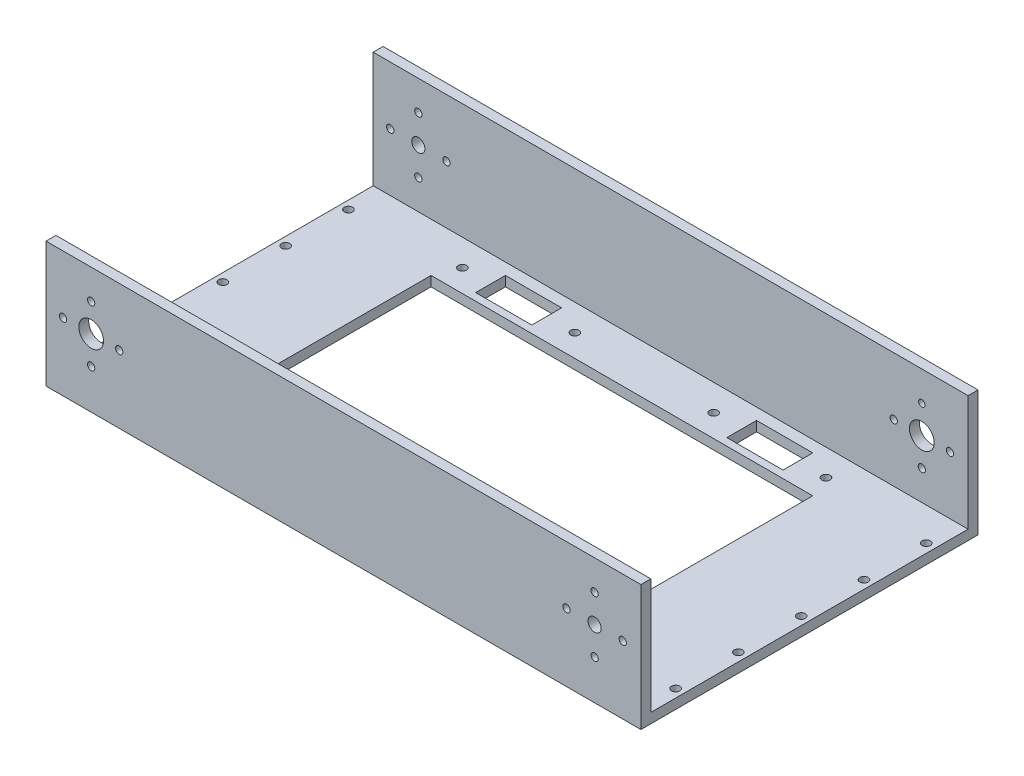
SolidWorks part; units mm, degrees
ref_plane "Front Plane" through (0, 0, 0) normal (0, 0, 1) x (1, 0, 0)
ref_plane "Top Plane" through (0, 0, 0) normal (0, 1, 0) x (1, 0, 0)
ref_plane "Right Plane" through (0, 0, 0) normal (1, 0, 0) x (0, 0, -1)
sketch "스케치1" plane through (0, 0, 0) normal (0, 0, 1) x (1, 0, 0)
  line L1 (-90, 17.5) -> (90, 17.5)
  line L2 (-90, 17.5) -> (-90, -17.5)
  line L3 (-90, -17.5) -> (90, -17.5)
  line L4 (90, 17.5) -> (90, -17.5)
  dimension "D1" = 17.5
  dimension "D2" = 35
  dimension "D3" = 90
  dimension "D4" = 180
extrude "보스-돌출1" add sketch "스케치1" along normal blind 3
sketch "스케치2" plane through (0, 0, 3) normal (0, 0, 1) x (1, 0, 0)
  line L0 (0, 0) -> (50000, 0) construction
  line L1 (0, 0) -> (0, -50000) construction
  line L2 (-76, 0) -> (-76, -50000) construction
  line L3 (76, 0) -> (76, -50000) construction
  circle A0 centre (-76.34, 0) radius 3.75
  circle A1 centre (76, 0) radius 2
  dimension "D3" = 7.5
  dimension "D4" = 4
  dimension "D1" = 76
  dimension "D2" = 76
extrude "컷-돌출1" cut sketch "스케치2" against normal blind 3
sketch "스케치3" plane through (0, 0, 3) normal (0, 0, 1) x (1, 0, 0)
  line L0 (-76.34, 0) -> (-76.34, 50000) construction
  line L1 (76, 0) -> (76, 50000) construction
  line L2 (-76.34, 0) -> (49923.66, 0) construction
  circle A0 centre (-76.34, 0) radius 8.5 construction
  circle A1 centre (76, 0) radius 8.5 construction
  circle A2 centre (-76.34, 8.5) radius 1.1
  circle A3 centre (-76.34, -8.5) radius 1.1
  circle A4 centre (-84.84, 0) radius 1.1
  circle A5 centre (-67.84, 0) radius 1.1
  circle A6 centre (76, 8.5) radius 1.1
  circle A7 centre (76, -8.5) radius 1.1
  circle A8 centre (67.5, 0) radius 1.1
  circle A9 centre (84.5, 0) radius 1.1
extrude "컷-돌출2" cut sketch "스케치3" against normal blind 3
sketch "스케치4" plane through (0, -17.5, 0) normal (0, -1, 0) x (1, 0, 0)
  line L0 (-90, 0) -> (-90, 50000) construction
  line L1 (90, 0) -> (90, 50000) construction
  line L2 (-100, 3) -> (49900, 3) construction
  line L6 (-100, -96) -> (49900, -96) construction
  line L7 (-100, -99) -> (49900, -99) construction
  line L8 (-100, 0) -> (49900, 0) construction
  line L11 (90, 3) -> (-90, 3)
  line L12 (90, 3) -> (90, -99)
  line L13 (90, -99) -> (-90, -99)
  line L14 (-90, 3) -> (-90, -99)
  dimension "D1" = 3
  dimension "D2" = 96
extrude "보스-돌출2" add sketch "스케치4" along normal blind 3
sketch "스케치5" plane through (0, -17.5, 0) normal (0, 1, 0) x (1, 0, 0)
  line L0 (-100, 99) -> (49900, 99) construction
  line L1 (86.532, 96) -> (50086.532, 96) construction
  line L2 (-90, 0) -> (-90, 50000) construction
  line L3 (-90, 0) -> (-90, 99) construction
  line L4 (90, 0) -> (90, 50000) construction
  line L7 (-90, 99) -> (90, 99)
  line L8 (-90, 99) -> (-90, 96)
  line L9 (-90, 96) -> (90, 96)
  line L10 (90, 99) -> (90, 96)
  dimension "D1" = 3
extrude "보스-돌출3" add sketch "스케치5" along normal blind 35
sketch "스케치6" plane through (0, 0, -99) normal (0, 0, -1) x (-1, 0, 0)
  circle A0 centre (-76, 0) radius 3.75
  circle A1 centre (76.34, 0) radius 2
  circle A2 centre (-76, -8.5) radius 1.1
  circle A3 centre (-67.5, 0) radius 1.1
  circle A4 centre (-76, 8.5) radius 0.9817
  circle A5 centre (-84.5, 0) radius 1.1
  circle A6 centre (84.84, 0) radius 1.1
  circle A7 centre (76.34, 8.5) radius 1.1
  circle A8 centre (67.84, 0) radius 1.1
  circle A9 centre (76.34, -8.5) radius 1.1
  dimension "D1" = 4
extrude "컷-돌출3" cut sketch "스케치6" against normal blind 35
sketch "스케치9" plane through (0, -17.5, 0) normal (0, 1, 0) x (1, 0, 0)
  line L0 (-0.8224, 48) -> (49999.1776, 48) construction
  line L1 (0, 0) -> (0, 50000) construction
  line L2 (90, 0) -> (-90, 0) construction
  line L4 (-57.75, 81.25) -> (57.75, 81.25)
  line L5 (-57.75, 81.25) -> (-57.75, 14.75)
  line L6 (-57.75, 14.75) -> (57.75, 14.75)
  line L7 (57.75, 81.25) -> (57.75, 14.75)
  dimension "D1" = 48
  dimension "D2" = 66.5
  dimension "D3" = 115.5
  dimension "D4" = 57.75
  dimension "D5" = 33.25
extrude "컷-돌출4" cut sketch "스케치9" against normal blind 10
sketch "스케치10" plane through (0, -20.5, 0) normal (0, -1, 0) x (1, 0, 0)
  line L0 (-10.9491, -48) -> (49989.0509, -48) construction
  line L1 (0, -34.9167) -> (0, -50034.9167) construction
  line L2 (-55, -10.9771) -> (-55, -50010.9771) construction
  line L3 (55, 8.1375) -> (55, -49991.8625) construction
  line L4 (-54.3745, -8) -> (49945.6255, -8) construction
  line L5 (75.9016, -88) -> (50075.9016, -88) construction
  line L6 (-90, 3) -> (-90, -99) construction
  line L7 (-90, -96) -> (90, -96) construction
  circle A0 centre (-55, -8) radius 1.25
  circle A1 centre (55, -8) radius 1.25
  circle A2 centre (55, -88) radius 1.25
  circle A3 centre (-55, -88) radius 1.25
  dimension "D1" = 90
  dimension "D2" = 48
  dimension "D3" = 55
  dimension "D4" = 55
  dimension "D5" = 40
  dimension "D6" = 40
extrude "컷-돌출5" cut sketch "스케치10" against normal blind 10
sketch "스케치11" plane through (0, -20.5, 0) normal (0, -1, 0) x (1, 0, 0)
  line L0 (55, -8) -> (-49945, -8) construction
  line L1 (55, -8) -> (55, -50008) construction
  line L2 (-55, -88) -> (-55, 49912) construction
  line L3 (-55, -88) -> (49945, -88) construction
  line L4 (38, -39.7065) -> (38, -50039.7065) construction
  line L5 (-38, -46.9547) -> (-38, -50046.9547) construction
  line L6 (21, -25.4517) -> (21, -50025.4517) construction
  line L7 (-21, -44.297) -> (-21, -50044.297) construction
  line L9 (46.5, -83.5) -> (29.5, -83.5)
  line L10 (46.5, -83.5) -> (46.5, -92.5)
  line L11 (46.5, -92.5) -> (29.5, -92.5)
  line L12 (29.5, -83.5) -> (29.5, -92.5)
  line L13 (-29.5, -83.5) -> (-46.5, -83.5)
  line L14 (-29.5, -83.5) -> (-29.5, -92.5)
  line L15 (-29.5, -92.5) -> (-46.5, -92.5)
  line L16 (-46.5, -83.5) -> (-46.5, -92.5)
  line L17 (46.5, -3.5) -> (29.5, -3.5)
  line L18 (46.5, -3.5) -> (46.5, -12.5)
  line L19 (46.5, -12.5) -> (29.5, -12.5)
  line L20 (29.5, -3.5) -> (29.5, -12.5)
  line L21 (-29.5, -3.5) -> (-46.5, -3.5)
  line L22 (-29.5, -3.5) -> (-29.5, -12.5)
  line L23 (-29.5, -12.5) -> (-46.5, -12.5)
  line L24 (-46.5, -3.5) -> (-46.5, -12.5)
  circle A0 centre (21, -8) radius 1.25
  circle A1 centre (-21, -8) radius 1.25
  circle A2 centre (21, -88) radius 1.25
  circle A3 centre (-21, -88) radius 1.25
  dimension "D5" = 17
  dimension "D1" = 17
  dimension "D2" = 17
  dimension "D3" = 17
  dimension "D4" = 17
  dimension "D6" = 9
  dimension "D7" = 9
  dimension "D8" = 17
  dimension "D9" = 17
  dimension "D10" = 9
  dimension "D11" = 17
  dimension "D12" = 9
  dimension "D13" = 8.5
  dimension "D14" = 4.5
  dimension "D15" = 4.5
  dimension "D16" = 8.5
  dimension "D17" = 4.5
  dimension "D18" = 8.5
  dimension "D19" = 8.5
  dimension "D20" = 4.5
extrude "컷-돌출6" cut sketch "스케치11" against normal blind 10
sketch "스케치12" plane through (0, -17.5, 0) normal (0, 1, 0) x (1, 0, 0)
  line L0 (-109.1605, 48) -> (49890.8395, 48) construction
  line L1 (-127.9882, 67) -> (49872.0118, 67) construction
  line L2 (-128.3888, 10) -> (49871.6112, 10) construction
  line L3 (-116.1709, 29) -> (49883.8291, 29) construction
  line L4 (-111.9647, 86) -> (49888.0353, 86) construction
  line L5 (-87.5, 63.4227) -> (-87.5, -49936.5773) construction
  line L6 (87.5, 65.6259) -> (87.5, -49934.3741) construction
  line L7 (90, 0) -> (-90, 0) construction
  line L9 (-90, 0) -> (-90, 96) construction
  line L10 (90, 96) -> (90, 0) construction
  circle A0 centre (-87.5, 86) radius 1.25
  circle A1 centre (-87.5, 67) radius 1.25
  circle A2 centre (-87.5, 48) radius 1.25
  circle A3 centre (-87.5, 29) radius 1.25
  circle A4 centre (-87.5, 10) radius 1.25
  circle A5 centre (87.3284, 86) radius 1.25
  circle A6 centre (87.5, 67) radius 1.25
  circle A7 centre (87.5, 48) radius 1.25
  circle A8 centre (87.5, 29) radius 1.25
  circle A9 centre (87.5, 10) radius 1.25
  dimension "D1" = 48
  dimension "D2" = 38
  dimension "D3" = 38
  dimension "D4" = 19
  dimension "D5" = 19
  dimension "D6" = 2.5
  dimension "D7" = 2.5
extrude "컷-돌출7" cut sketch "스케치12" against normal blind 10
